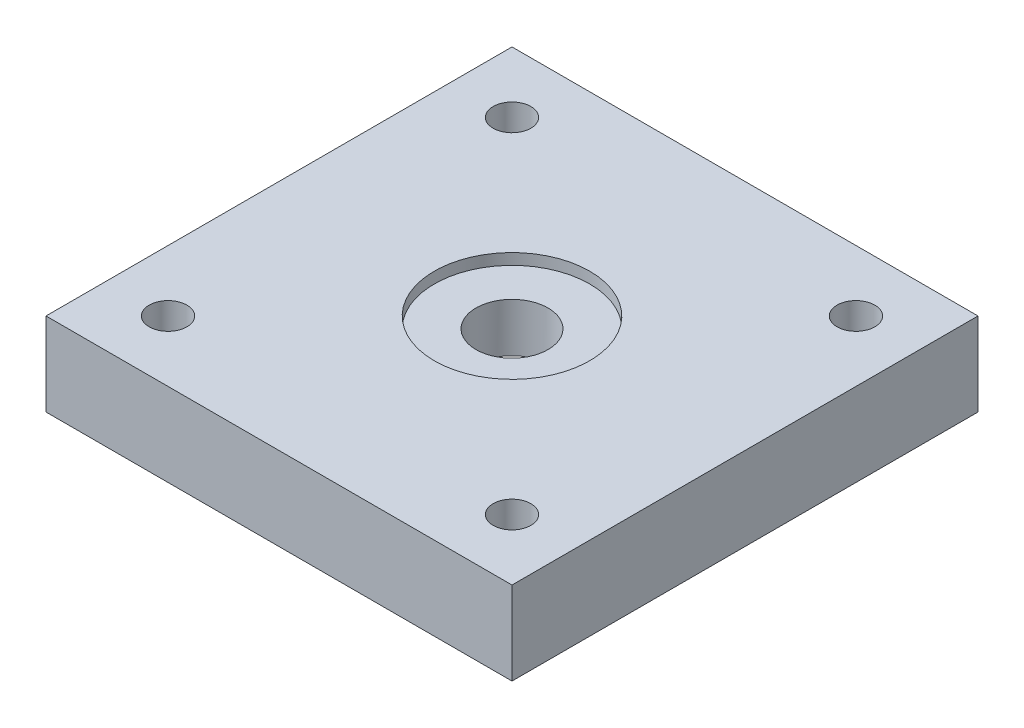
SolidWorks part; units mm, degrees
material "6061 Alloy"
ref_plane "Front Plane" through (0, 0, 0) normal (0, 0, 1) x (1, 0, 0)
ref_plane "Top Plane" through (0, 0, 0) normal (0, 1, 0) x (1, 0, 0)
ref_plane "Right Plane" through (0, 0, 0) normal (1, 0, 0) x (0, 0, -1)
sketch "Sketch1" plane through (0, 0, 0) normal (0, 1, 0) x (1, 0, 0)
  line L1 (-21, -21) -> (21, -21)
  line L2 (-21, -21) -> (-21, 21)
  line L3 (-21, 21) -> (21, 21)
  line L4 (21, -21) -> (21, 21)
  line L5 (-21, -21) -> (21, 21) construction
  line L6 (-21, 21) -> (21, -21) construction
  circle A0 centre (-15.5, 15.5) radius 1.7
  circle A1 centre (15.5, 15.5) radius 1.7
  circle A2 centre (15.5, -15.5) radius 1.7
  circle A3 centre (-15.5, -15.5) radius 1.7
  point P0 (0, 0)
  dimension "D3" = 3.4
  dimension "D1" = 42
  dimension "D2" = 31
extrude "Boss-Extrude1" add sketch "Sketch1" along normal blind 7.5
sketch "Sketch2" plane through (0, 0, 0) normal (0, -1, 0) x (-1, 0, 0)
  circle A0 centre (0, 0) radius 11
  dimension "D1" = 22
extrude "Cut-Extrude1" cut sketch "Sketch2" against normal blind 2.1
sketch "Sketch3" plane through (0, 7.5, 0) normal (0, 1, 0) x (1, 0, 0)
  circle A0 centre (0, 0) radius 7
  dimension "D1" = 14
extrude "Cut-Extrude2" cut sketch "Sketch3" against normal blind 1
sketch "Sketch4" plane through (0, 6.5, 0) normal (0, 1, 0) x (1, 0, 0)
  circle A0 centre (0, 0) radius 3.25
  dimension "D1" = 6.5
extrude "Cut-Extrude3" cut sketch "Sketch4" against normal blind 10
